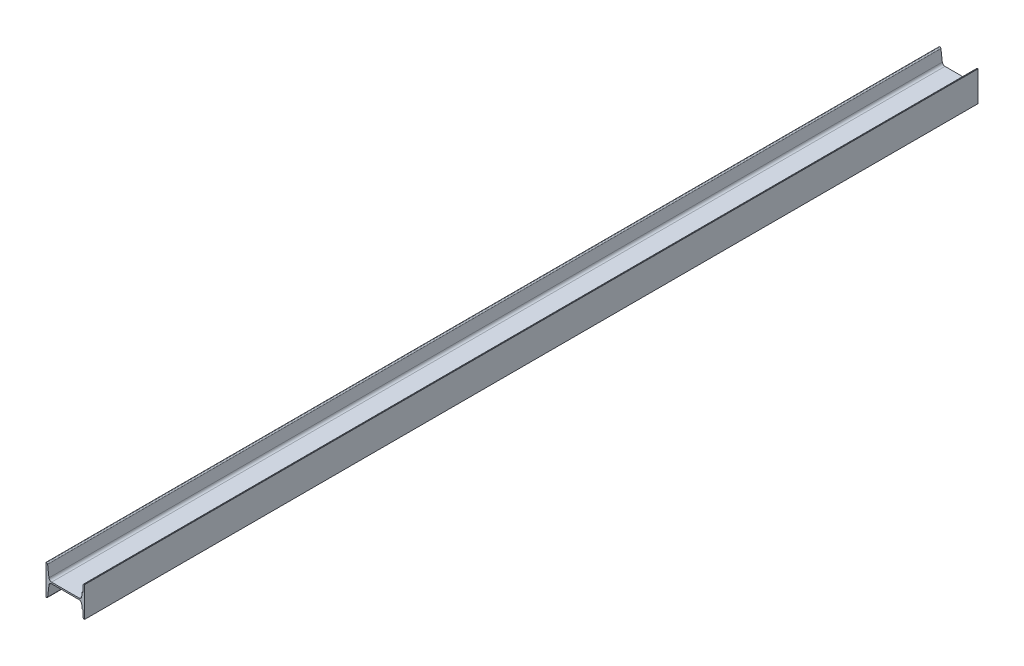
SolidWorks part; units mm, degrees
ref_plane "Front Plane" through (0, 0, 0) normal (0, 0, 1) x (1, 0, 0)
ref_plane "Top Plane" through (0, 0, 0) normal (0, 1, 0) x (1, 0, 0)
ref_plane "Right Plane" through (0, 0, 0) normal (1, 0, 0) x (0, 0, -1)
ref_plane "Plane1" through (0, 0, 1800) normal (0, 0, 1) x (1, 0, 0)
sketch "Sketch1" plane through (0, 0, 1800) normal (0, 0, 1) x (1, 0, 0)
  line L0 (129, 60.4688) -> (129, 30)
  line L1 (129, 30) -> (124.9197, 30)
  line L2 (124.9197, 30) -> (122.7927, 12.6894)
  line L3 (111.8711, 3) -> (-1.8711, 3)
  line L4 (-12.7927, 12.6894) -> (-18.2943, 58.5362)
  line L5 (-22.7623, 62.5) -> (-25, 62.5)
  line L6 (-25, 62.5) -> (-25, -62.5)
  line L7 (-25, -62.5) -> (-22.7623, -62.5)
  line L8 (-18.2943, -58.5362) -> (-12.7927, -12.6894)
  line L9 (-1.8711, -3) -> (111.8711, -3)
  line L10 (122.7927, -12.6894) -> (124.87, -30)
  line L11 (124.87, -30) -> (129, -30)
  line L12 (129, -30) -> (129, -60.4688)
  line L13 (132.7623, -62.5) -> (135, -62.5)
  line L14 (135, -62.5) -> (135, 62.5)
  line L15 (135, 62.5) -> (132.7623, 62.5)
  arc A0 (122.7927, 12.6894) -> (111.8711, 3) centre (111.8711, 14) cw
  arc A1 (-1.8711, 3) -> (-12.7927, 12.6894) centre (-1.8711, 14) cw
  arc A2 (-18.2943, 58.5362) -> (-22.7623, 62.5) centre (-22.7623, 58) ccw
  arc A3 (-22.7623, -62.5) -> (-18.2943, -58.5362) centre (-22.7623, -58) ccw
  arc A4 (-12.7927, -12.6894) -> (-1.8711, -3) centre (-1.8711, -14) cw
  arc A5 (111.8711, -3) -> (122.7927, -12.6894) centre (111.8711, -14) cw
  arc A6 (129, -60.4688) -> (132.7623, -62.5) centre (132.7623, -58) ccw
  arc A7 (132.7623, 62.5) -> (129, 60.4688) centre (132.7623, 58) ccw
extrude "Boss-Extrude1" add sketch "Sketch1" against normal blind 3700
scale "Scale1" scale about centroid uniform scaling yes scale factor 0.75
sketch "Sketch2" plane through (0, 0, -1437.5) normal (0, 0, -1) x (-1, 0, 0)
